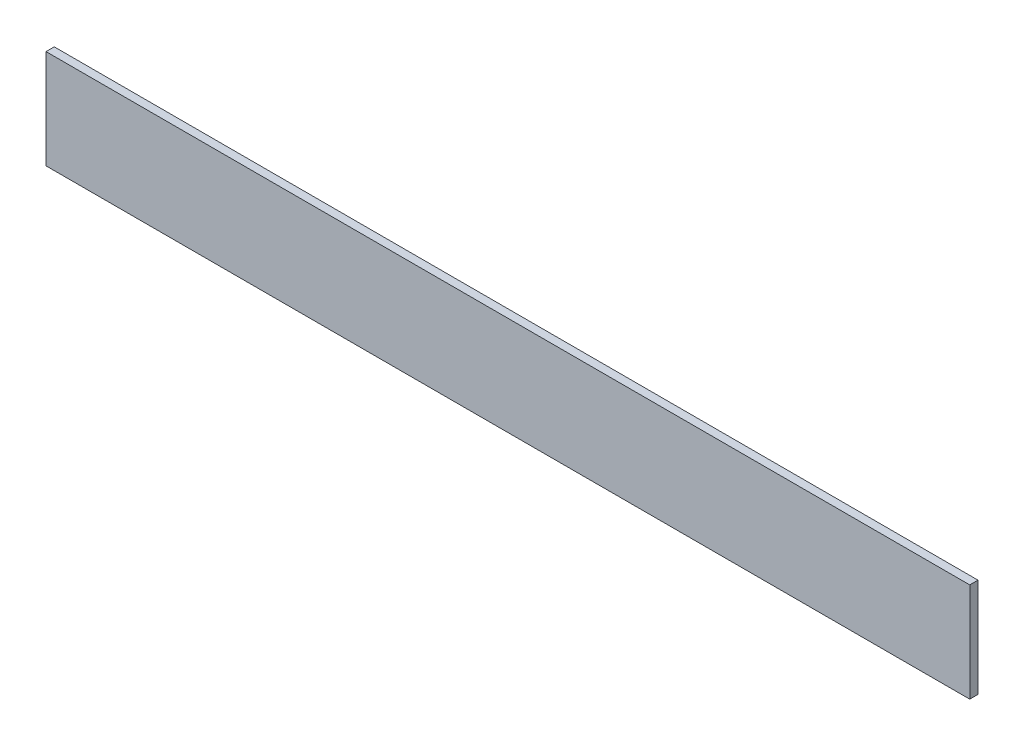
SolidWorks part; units mm, degrees
material "PVC 0.007 Plasticized"
ref_plane "Front Plane" through (0, 0, 0) normal (0, 0, 1) x (1, 0, 0)
ref_plane "Top Plane" through (0, 0, 0) normal (0, 1, 0) x (1, 0, 0)
ref_plane "Right Plane" through (0, 0, 0) normal (1, 0, 0) x (0, 0, -1)
sketch "Sketch1" plane through (0, 0, 0) normal (1, 0, 0) x (0, 0, -1)
  line L1 (-3.175, -38.1) -> (3.175, -38.1)
  line L2 (-3.175, -38.1) -> (-3.175, 38.1)
  line L3 (-3.175, 38.1) -> (3.175, 38.1)
  line L4 (3.175, -38.1) -> (3.175, 38.1)
  line L5 (-3.175, -38.1) -> (3.175, 38.1) construction
  line L6 (-3.175, 38.1) -> (3.175, -38.1) construction
  point P0 (0, 0)
  dimension "D1" = 76.2
  dimension "D2" = 6.35
extrude "Boss-Extrude1" add sketch "Sketch1" along normal blind 711.2
equation "\"D2@Sketch1\"=1in/4"
